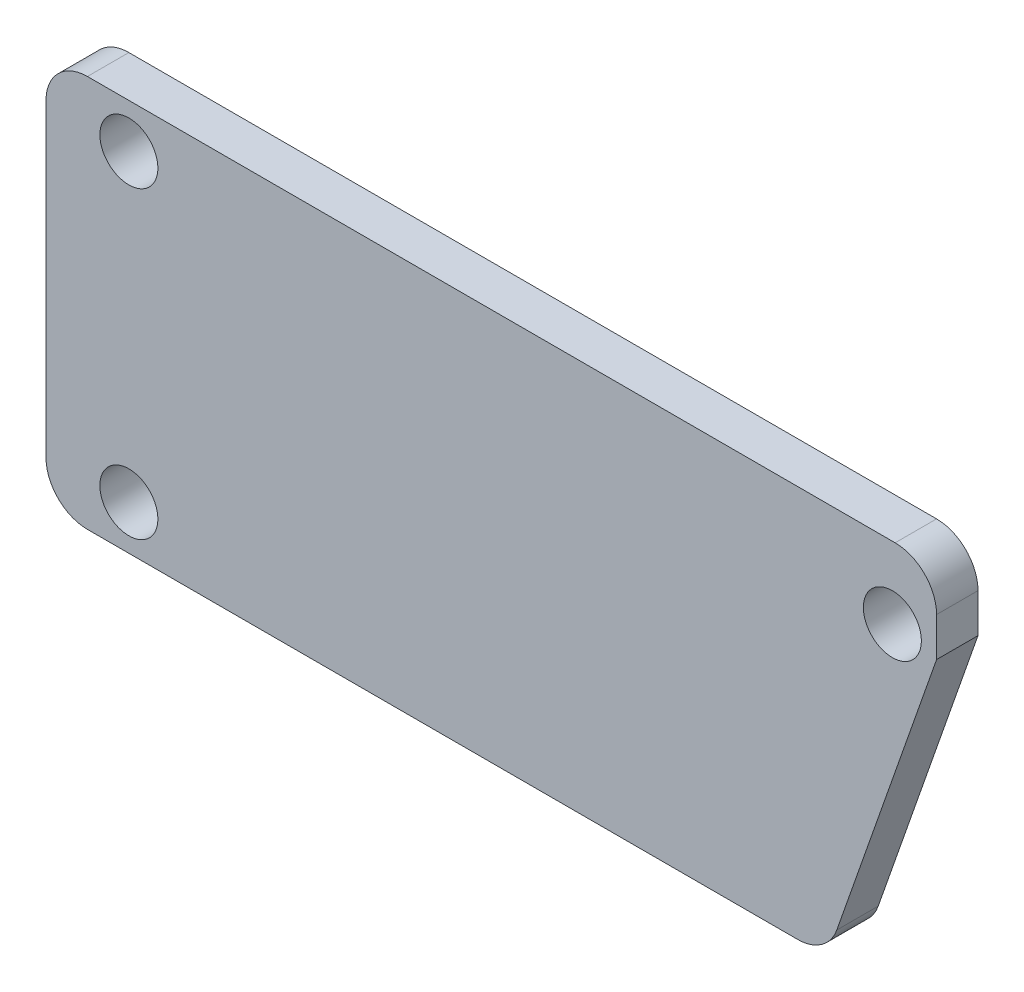
SolidWorks part; units mm, degrees
ref_plane "Plan de face" through (0, 0, 0) normal (0, 0, 1) x (1, 0, 0)
ref_plane "Plan de dessus" through (0, 0, 0) normal (0, 1, 0) x (1, 0, 0)
ref_plane "Plan de droite" through (0, 0, 0) normal (1, 0, 0) x (0, 0, -1)
sketch "Esquisse1" plane through (0, 0, 0) normal (0, 0, 1) x (1, 0, 0)
  line L0 (-8.9522, 1.1125) -> (22.7878, 1.1125) construction
  line L1 (-8.9522, 8.2125) -> (23.2878, 8.2125)
  line L2 (-8.9522, 8.2125) -> (-8.9522, -5.9875)
  line L3 (-8.9522, -5.9875) -> (19.3231, -5.9875)
  line L4 (23.2878, 8.2125) -> (23.2878, 5.3016)
  line L5 (19.3231, -5.9875) -> (23.2878, 5.3016)
  circle A0 centre (-5.9522, -4.3875) radius 1.05
  circle A1 centre (-5.9522, 6.6125) radius 1.05
  circle A2 centre (21.6878, 5.6125) radius 1.05
  point P1 (19.3231, -5.9875)
  point P14 (18.8418, -6.1269)
  dimension "D3" = 2.1
  dimension "D1" = 14.2
  dimension "D2" = 11
  dimension "D4" = 1
  dimension "D5" = 27.64
  dimension "D6" = 1.6
  dimension "D7" = 3
extrude "Boss.-Extru.1" add sketch "Esquisse1" along normal blind 1.5
fillet "Congé1" radius 1.5 1 edges at (23.2878, 8.2125, 0.75)
fillet "Congé2" radius 1.5 3 edges at (19.3231, -5.9875, 0.75) (-8.9522, -5.9875, 0.75) (-8.9522, 8.2125, 0.75)
sketch "Esquisse3" plane through (0, 0, 0) normal (0, 0, -1) x (-1, 0, 0)
  line L0 (-23.2878, 5.3016) -> (-23.2878, 6.7125) construction
  line L1 (-5.2078, 2.3625) -> (-2.7078, 2.3625)
  line L2 (-5.2078, 2.3625) -> (-5.2078, -0.1375)
  line L3 (-5.2078, -0.1375) -> (-2.7078, -0.1375)
  line L4 (-2.7078, 2.3625) -> (-2.7078, -0.1375)
  line L5 (-5.2078, 1.1125) -> (-2.7078, 1.1125) construction
  line L6 (7.4522, -5.9875) -> (-18.2601, -5.9875) construction
  line L7 (-21.7878, 8.2125) -> (7.4522, 8.2125) construction
  dimension "D1" = 2.5
  dimension "D2" = 2.5
  dimension "D3" = 18.08
extrude "Boss.-Extru.2" add sketch "Esquisse3" along normal blind 2
